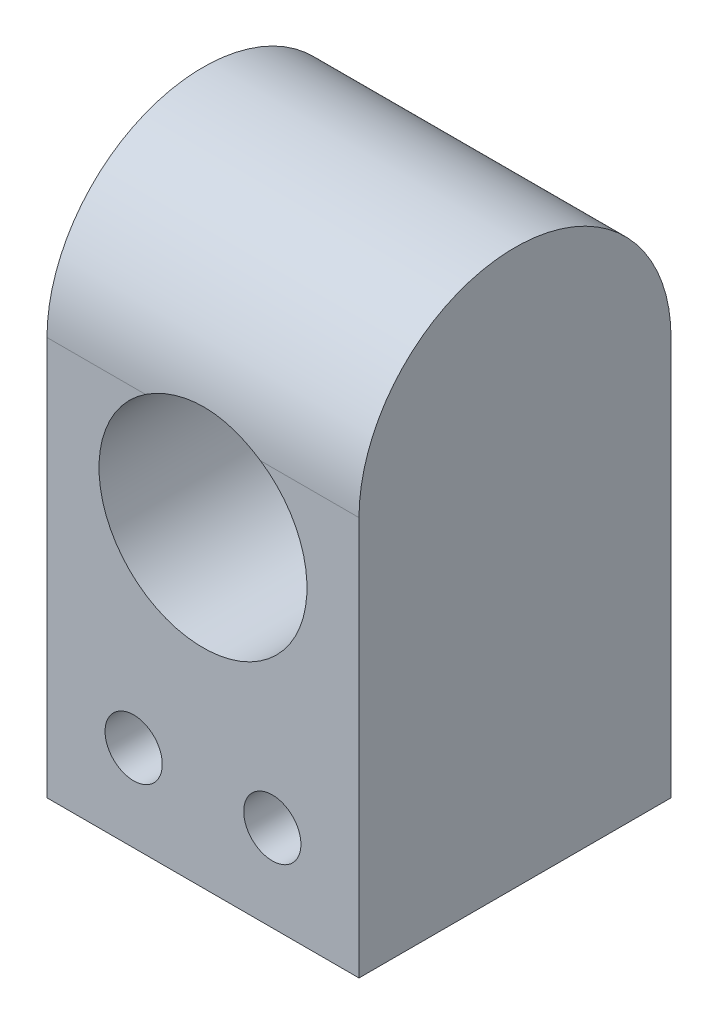
SolidWorks part; units mm, degrees
ref_plane "Front Plane" through (0, 0, 0) normal (0, 0, 1) x (1, 0, 0)
ref_plane "Top Plane" through (0, 0, 0) normal (0, 1, 0) x (1, 0, 0)
ref_plane "Right Plane" through (0, 0, 0) normal (1, 0, 0) x (0, 0, -1)
sketch "Sketch1" plane through (0, 0, 0) normal (1, 0, 0) x (0, 0, -1)
  line L1 (-9, -11.5) -> (9, -11.5)
  line L2 (-9, -11.5) -> (-9, 11.5)
  line L4 (9, -11.5) -> (9, 11.5)
  line L5 (-9, -11.5) -> (9, 11.5) construction
  line L6 (-9, 11.5) -> (9, -11.5) construction
  arc A0 (-9, 11.5) -> (9, 11.5) centre (0, 11.5) cw
  point P0 (0, 0)
  dimension "D1" = 9
  dimension "D2" = 23
extrude "Boss-Extrude1" add sketch "Sketch1" along normal blind 18
sketch "Sketch2" plane through (0, 0, 9) normal (0, 0, 1) x (1, 0, 0)
  line L0 (9, 6.5) -> (9, 20.5) construction
  line L1 (18, 20.5) -> (0, 20.5) construction
  circle A0 centre (9, 6.5) radius 6
  dimension "D1" = 12
  dimension "D2" = 14
extrude "Cut-Extrude1" cut sketch "Sketch2" against normal blind 18
sketch "Sketch3" plane through (0, 0, 9) normal (0, 0, 1) x (1, 0, 0)
  line L0 (5, -6.5) -> (13, -6.5) construction
  line L1 (9, 6.5) -> (9, -6.5) construction
  dimension "D1" = 8
  dimension "D2" = 13
hole_wizard "M4x0.7 Tapped Hole1" positions "Sketch4" profile "Sketch5" tap size "M4x0.7" standard "BSI" end condition through all
sketch "Sketch4" plane through (0, 0, 9) normal (0, 0, 1) x (1, 0, 0)
  point P0 (5, -6.5)
  point P3 (13, -6.5)
sketch "Sketch5" plane through (5, -6.5, 9) normal (1, 0, 0) x (0, -1, 0)
  line L0 (0, 0) -> (0, 18)
  line L1 (0, 18) -> (1.65, 18)
  line L2 (1.65, 18) -> (1.65, 0)
  line L5 (1.65, 0) -> (0, 0)
  line L11 (0, -6.35) -> (0, 107.95) construction
  dimension "Thru Tap Drill Dia." = 3.3
  dimension "Thru Tap Drill Depth" = 18
cosmetic thread "Hole Thread1" parameters "D2"=4
cosmetic thread "Hole Thread2" parameters "D2"=4
